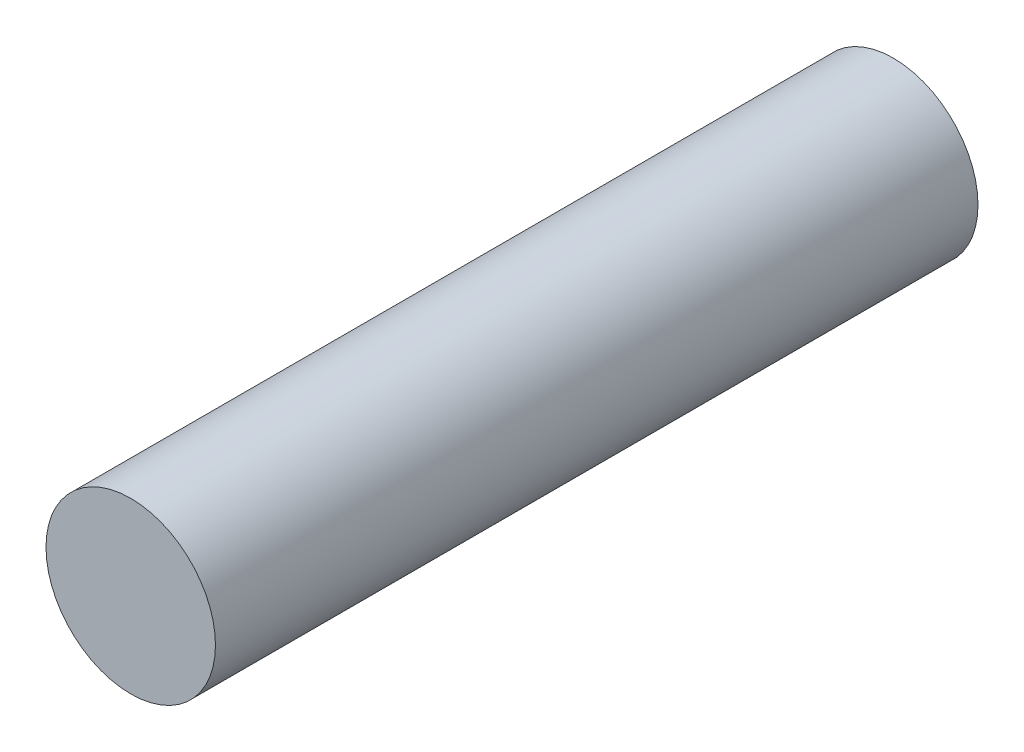
SolidWorks part; units mm, degrees
ref_plane "Front Plane" through (0, 0, 0) normal (0, 0, 1) x (1, 0, 0)
ref_plane "Top Plane" through (0, 0, 0) normal (0, 1, 0) x (1, 0, 0)
ref_plane "Right Plane" through (0, 0, 0) normal (1, 0, 0) x (0, 0, -1)
sketch "Sketch1" plane through (0, 0, 0) normal (0, 0, 1) x (1, 0, 0)
  circle A0 centre (0, 0) radius 10
  dimension "D1" = 20
extrude "Boss-Extrude1" add sketch "Sketch1" along normal mid plane 90
